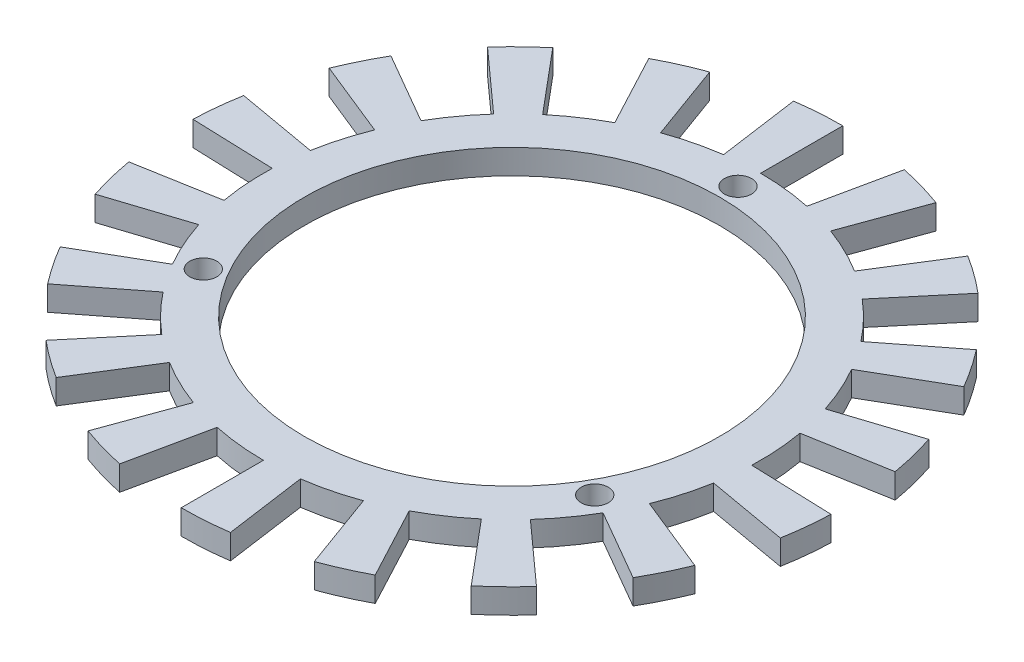
SolidWorks part; units mm, degrees
material "AISI 1010 Steel, hot rolled bar"
ref_plane "Front Plane" through (0, 0, 0) normal (0, 0, 1) x (1, 0, 0)
ref_plane "Top Plane" through (0, 0, 0) normal (0, 1, 0) x (1, 0, 0)
ref_plane "Right Plane" through (0, 0, 0) normal (1, 0, 0) x (0, 0, -1)
sketch "Sketch1" plane through (0, 0, 0) normal (0, 1, 0) x (1, 0, 0)
  circle A0 centre (0, 0) radius 25.25
  dimension "D1" = 50.5
extrude "Extrude-Thin1" add sketch "Sketch1" against normal blind 3 thin
sketch "Sketch2" plane through (0, 0, 0) normal (0, 1, 0) x (1, 0, 0)
  line L0 (0, -30.25) -> (0, 30.25) construction
  line L1 (0, 0) -> (23.8157, -13.75) construction
  line L2 (0, 0) -> (-23.8157, -13.75) construction
  circle A0 centre (0, 27.5) radius 1.65
  circle A1 centre (0, 0) radius 30.25 construction
  circle A4 centre (0, 0) radius 27.5 construction
  circle A7 centre (23.8157, -13.75) radius 1.65
  circle A8 centre (-23.8157, -13.75) radius 1.65
  dimension "D1" = 55
  dimension "D2" = 3.3
  dimension "D3" = 120
  dimension "D4" = 120
extrude "Cut-Extrude3" cut sketch "Sketch2" against normal blind 10
sketch "Sketch5" plane through (0, -3, 0) normal (0, -1, 0) x (1, 0, 0)
  line L0 (0, 0) -> (0, 35.9971) construction
  line L1 (0, 0) -> (4.7467, 33.7749) construction
  line L2 (0, 40.25) -> (0, 30.25)
  line L3 (4.21, 29.9556) -> (5.6017, 39.8583)
  line L4 (13.7663, 37.8226) -> (10.3461, 28.4257)
  line L5 (14.2015, 26.7092) -> (18.8962, 35.5386)
  line L6 (25.8722, 30.8333) -> (19.4443, 23.1728)
  line L7 (22.4801, 20.2412) -> (29.9116, 26.9325)
  line L8 (34.8575, 20.125) -> (26.1973, 15.125)
  line L9 (28.0473, 11.3318) -> (37.3192, 15.0779)
  line L10 (39.6385, 6.9893) -> (29.7904, 5.2529)
  line L11 (30.2316, 1.0557) -> (40.2255, 1.4047)
  line L12 (39.6385, -6.9893) -> (29.7904, -5.2529)
  line L13 (28.7695, -9.3478) -> (38.28, -12.4379)
  line L14 (34.8575, -20.125) -> (26.1973, -15.125)
  line L15 (23.8373, -18.6238) -> (31.7174, -24.7804)
  line L16 (25.8722, -30.8333) -> (19.4443, -23.1728)
  line L17 (16.0301, -25.6535) -> (21.3293, -34.1339)
  line L18 (13.7663, -37.8226) -> (10.3461, -28.4257)
  line L19 (6.2893, -29.589) -> (8.3684, -39.3704)
  line L20 (0, -40.25) -> (0, -30.25)
  line L21 (-4.21, -29.9556) -> (-5.6017, -39.8583)
  line L48 (-13.7663, -37.8226) -> (-10.3461, -28.4257)
  line L49 (-14.2015, -26.7092) -> (-18.8962, -35.5386)
  line L50 (-25.8722, -30.8333) -> (-19.4443, -23.1728)
  line L51 (-22.4801, -20.2412) -> (-29.9116, -26.9325)
  line L52 (-34.8575, -20.125) -> (-26.1973, -15.125)
  line L53 (-28.0473, -11.3318) -> (-37.3192, -15.0779)
  line L54 (-39.6385, -6.9893) -> (-29.7904, -5.2529)
  line L55 (-30.2316, -1.0557) -> (-40.2255, -1.4047)
  line L56 (-39.6385, 6.9893) -> (-29.7904, 5.2529)
  line L57 (-28.7695, 9.3478) -> (-38.28, 12.4379)
  line L58 (-34.8575, 20.125) -> (-26.1973, 15.125)
  line L59 (-23.8373, 18.6238) -> (-31.7174, 24.7804)
  line L60 (-25.8722, 30.8333) -> (-19.4443, 23.1728)
  line L61 (-16.0301, 25.6535) -> (-21.3293, 34.1339)
  line L62 (-13.7663, 37.8226) -> (-10.3461, 28.4257)
  line L63 (-6.2893, 29.589) -> (-8.3684, 39.3704)
  circle A0 centre (0, 0) radius 30.25 construction
  arc A1 (4.21, 29.9556) -> (0, 30.25) centre (0, 0) ccw
  arc A2 (5.6017, 39.8583) -> (0, 40.25) centre (0, 0) ccw
  arc A3 (18.8962, 35.5386) -> (13.7663, 37.8226) centre (0, 0) ccw
  arc A4 (14.2015, 26.7092) -> (10.3461, 28.4257) centre (0, 0) ccw
  arc A5 (29.9116, 26.9325) -> (25.8722, 30.8333) centre (0, 0) ccw
  arc A6 (22.4801, 20.2412) -> (19.4443, 23.1728) centre (0, 0) ccw
  arc A7 (37.3192, 15.0779) -> (34.8575, 20.125) centre (0, 0) ccw
  arc A8 (28.0473, 11.3318) -> (26.1973, 15.125) centre (0, 0) ccw
  arc A9 (40.2255, 1.4047) -> (39.6385, 6.9893) centre (0, 0) ccw
  arc A10 (30.2316, 1.0557) -> (29.7904, 5.2529) centre (0, 0) ccw
  arc A11 (38.28, -12.4379) -> (39.6385, -6.9893) centre (0, 0) ccw
  arc A12 (28.7695, -9.3478) -> (29.7904, -5.2529) centre (0, 0) ccw
  arc A13 (31.7174, -24.7804) -> (34.8575, -20.125) centre (0, 0) ccw
  arc A14 (23.8373, -18.6238) -> (26.1973, -15.125) centre (0, 0) ccw
  arc A15 (21.3293, -34.1339) -> (25.8722, -30.8333) centre (0, 0) ccw
  arc A16 (16.0301, -25.6535) -> (19.4443, -23.1728) centre (0, 0) ccw
  arc A17 (8.3684, -39.3704) -> (13.7663, -37.8226) centre (0, 0) ccw
  arc A18 (6.2893, -29.589) -> (10.3461, -28.4257) centre (0, 0) ccw
  arc A19 (-5.6017, -39.8583) -> (0, -40.25) centre (0, 0) ccw
  arc A20 (-4.21, -29.9556) -> (0, -30.25) centre (0, 0) ccw
  arc A47 (-18.8962, -35.5386) -> (-13.7663, -37.8226) centre (0, 0) ccw
  arc A48 (-14.2015, -26.7092) -> (-10.3461, -28.4257) centre (0, 0) ccw
  arc A49 (-29.9116, -26.9325) -> (-25.8722, -30.8333) centre (0, 0) ccw
  arc A50 (-22.4801, -20.2412) -> (-19.4443, -23.1728) centre (0, 0) ccw
  arc A51 (-37.3192, -15.0779) -> (-34.8575, -20.125) centre (0, 0) ccw
  arc A52 (-28.0473, -11.3318) -> (-26.1973, -15.125) centre (0, 0) ccw
  arc A53 (-40.2255, -1.4047) -> (-39.6385, -6.9893) centre (0, 0) ccw
  arc A54 (-30.2316, -1.0557) -> (-29.7904, -5.2529) centre (0, 0) ccw
  arc A55 (-38.28, 12.4379) -> (-39.6385, 6.9893) centre (0, 0) ccw
  arc A56 (-28.7695, 9.3478) -> (-29.7904, 5.2529) centre (0, 0) ccw
  arc A57 (-31.7174, 24.7804) -> (-34.8575, 20.125) centre (0, 0) ccw
  arc A58 (-23.8373, 18.6238) -> (-26.1973, 15.125) centre (0, 0) ccw
  arc A59 (-21.3293, 34.1339) -> (-25.8722, 30.8333) centre (0, 0) ccw
  arc A60 (-16.0301, 25.6535) -> (-19.4443, 23.1728) centre (0, 0) ccw
  arc A61 (-8.3684, 39.3704) -> (-13.7663, 37.8226) centre (0, 0) ccw
  arc A62 (-6.2893, 29.589) -> (-10.3461, 28.4257) centre (0, 0) ccw
  point P87 (0, 0)
  dimension "D2" = 10
  dimension "D1" = 8
  dimension "D3" = 18
extrude "Boss-Extrude1" add sketch "Sketch5" against normal blind 3
